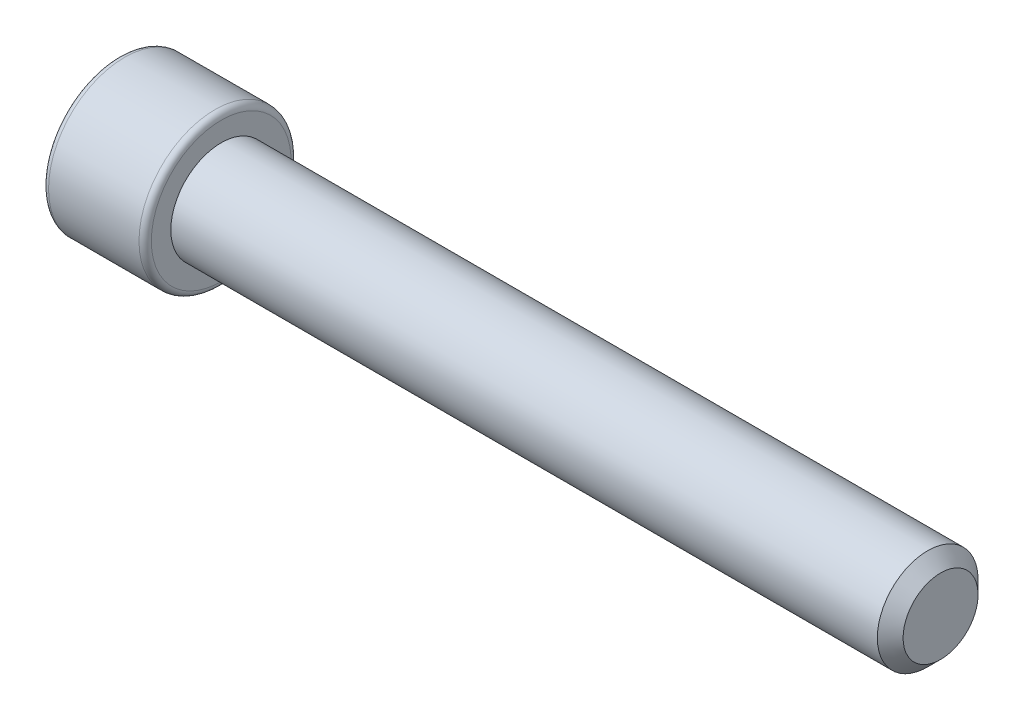
SolidWorks part; units mm, degrees
material "Galvanized Steel"
ref_plane "Front Plane" through (0, 0, 0) normal (0, 0, 1) x (1, 0, 0)
ref_plane "Top Plane" through (0, 0, 0) normal (0, 1, 0) x (1, 0, 0)
ref_plane "Right Plane" through (0, 0, 0) normal (1, 0, 0) x (0, 0, -1)
sketch "Sketch1" plane through (0, 0, 0) normal (0, 0, 1) x (1, 0, 0)
  line L0 (-24.5048, 0) -> (21.6751, 0) construction
  line L1 (0, 10.932) -> (0, -6.3293) construction
  line L2 (25.4, 0) -> (25.4, 3.1115)
  line L4 (25.4, 3.1115) -> (-19.05, 3.1115)
  line L5 (-19.05, 3.1115) -> (-19.05, 4.699)
  line L6 (-19.05, 4.699) -> (-25.4, 4.699)
  line L7 (-25.4, 4.699) -> (-25.4, 0)
  line L8 (-25.4, 0) -> (25.4, 0)
  dimension "D1" = 9.398
  dimension "D2" = 6.223
  dimension "D3" = 50.8
  dimension "D4" = 6.35
revolve "Revolve1" add sketch "Sketch1" angle 360 about L0
sketch "Sketch2" plane through (-25.4, 0, 0) normal (-1, 0, 0) x (0, 0, 1)
  line L0 (0, 5.0398) -> (0, -5.3552) construction
  line L1 (-5.6471, 0) -> (6.1045, 0) construction
  line L2 (0, 2.7496) -> (-2.3812, 1.3748)
  line L3 (-2.3812, 1.3748) -> (-2.3812, -1.3748)
  line L4 (-2.3812, -1.3748) -> (0, -2.7496)
  line L5 (0, -2.7496) -> (2.3812, -1.3748)
  line L6 (2.3812, -1.3748) -> (2.3812, 1.3748)
  line L7 (2.3812, 1.3748) -> (0, 2.7496)
  dimension "D1" = 5.4993
  dimension "D2" = 4.7625
  dimension "D3" = 2.7496
extrude "Extrude1" cut sketch "Sketch2" against normal blind 3.81
fillet "Fillet1" radius 0.381 2 edges at (-19.05, 0, 4.699) (-25.4, 0, 4.699)
chamfer "Chamfer1" distance 0.795 angle 45 1 edges at (25.4, 0, 3.1115)
